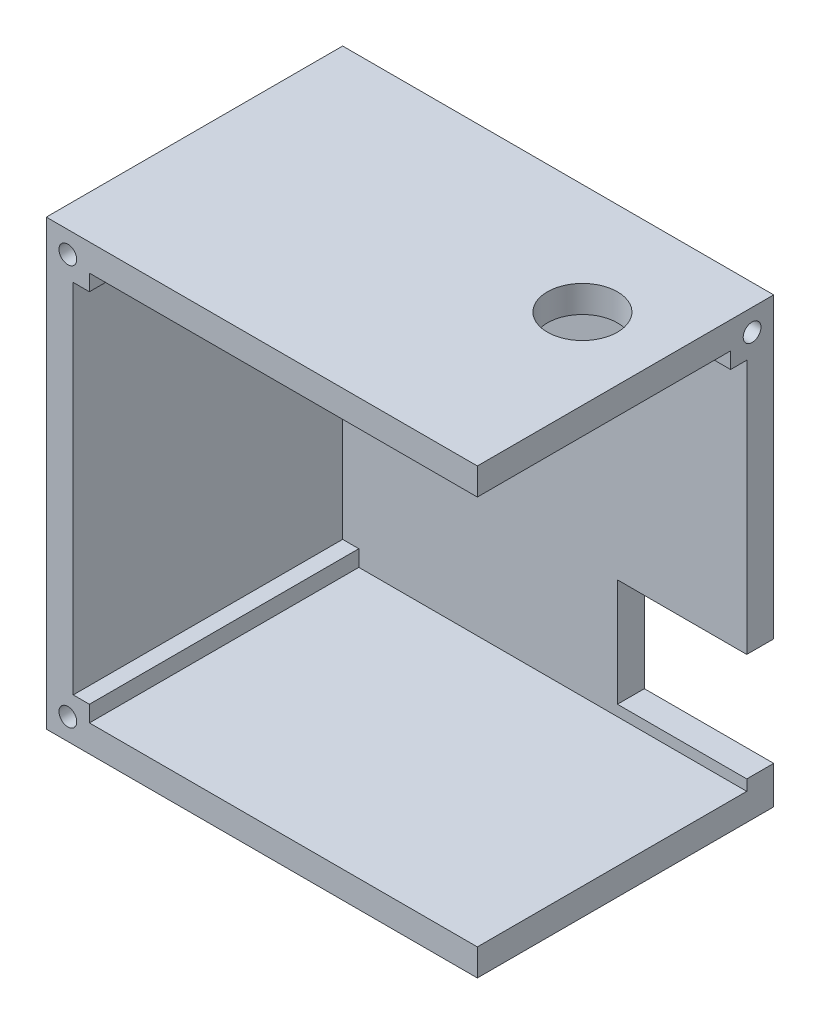
SolidWorks part; units mm, degrees
ref_plane "Front Plane" through (0, 0, 0) normal (0, 0, 1) x (1, 0, 0)
ref_plane "Top Plane" through (0, 0, 0) normal (0, 1, 0) x (1, 0, 0)
ref_plane "Right Plane" through (0, 0, 0) normal (1, 0, 0) x (0, 0, -1)
sketch "Sketch1" plane through (0, 0, 0) normal (0, 0, 1) x (1, 0, 0)
  line L1 (0, 0) -> (80, 0)
  line L2 (0, 0) -> (0, 82.3)
  line L3 (0, 82.3) -> (80, 82.3)
  line L4 (80, 0) -> (80, 82.3)
  dimension "D1" = 82.3
  dimension "D2" = 80
extrude "Boss-Extrude1" add sketch "Sketch1" along normal blind 55
sketch "Sketch2" plane through (0, 0, 55) normal (0, 0, 1) x (1, 0, 0)
  line L0 (80, 0) -> (80, 82.3) construction
  line L1 (5, 5) -> (80, 5) construction
  line L2 (5, 5) -> (5, 77.3) construction
  line L3 (5, 77.3) -> (80, 77.3) construction
  line L4 (80, 5) -> (80, 77.3)
  line L5 (80, 82.3) -> (0, 82.3) construction
  line L6 (0, 82.3) -> (0, 0) construction
  line L7 (5, 8) -> (5, 74.3)
  line L8 (5, 5) -> (8, 5) construction
  line L9 (5, 5) -> (5, 8) construction
  line L10 (5, 8) -> (8, 8)
  line L11 (8, 5) -> (8, 8)
  line L12 (5, 74.3) -> (8, 74.3)
  line L13 (5, 74.3) -> (5, 77.3) construction
  line L14 (5, 77.3) -> (8, 77.3) construction
  line L15 (8, 74.3) -> (8, 77.3)
  line L16 (8, 77.3) -> (80, 77.3)
  line L17 (8, 5) -> (80, 5)
  dimension "D1" = 5
  dimension "D2" = 5
  dimension "D3" = 5
  dimension "D4" = 3
extrude "Cut-Extrude1" cut sketch "Sketch2" against normal blind 50
sketch "Sketch3" plane through (0, 0, 55) normal (0, 0, 1) x (1, 0, 0)
  line L0 (4, 82.3) -> (4, 0) construction
  line L1 (80, 82.3) -> (0, 82.3) construction
  line L2 (0, 0) -> (80, 0) construction
  line L5 (0, 82.3) -> (0, 0) construction
  line L6 (4, 4) -> (4, 0) construction
  line L7 (4, 82.3) -> (4, 78.3) construction
  circle A0 centre (4, 78.3) radius 1.65
  circle A1 centre (4, 4) radius 1.65
  dimension "D3" = 3.3
  dimension "D1" = 4
  dimension "D2" = 4
extrude "Cut-Extrude2" cut sketch "Sketch3" against normal blind 25
sketch "Sketch4" plane through (0, 0, 5) normal (0, 0, 1) x (1, 0, 0)
  line L0 (5, 41.15) -> (80, 41.15) construction
  line L1 (5, 74.3) -> (5, 8) construction
  line L2 (80, 5) -> (80, 77.3) construction
  line L3 (8, 5) -> (80, 5) construction
  line L4 (10.5, 54.65) -> (25.5, 54.65)
  line L5 (10.5, 54.65) -> (10.5, 27.65)
  line L6 (10.5, 27.65) -> (25.5, 27.65)
  line L7 (25.5, 54.65) -> (25.5, 27.65)
  line L8 (56, 27) -> (80, 27)
  line L9 (56, 27) -> (56, 7)
  line L10 (56, 7) -> (80, 7)
  line L11 (80, 27) -> (80, 7)
  point P10 (25.5, 41.15)
  dimension "D1" = 27
  dimension "D2" = 15
  dimension "D3" = 5.5
  dimension "D4" = 24
  dimension "D5" = 20
  dimension "D6" = 2
extrude "Cut-Extrude3" cut sketch "Sketch4" against normal blind 20
sketch "Sketch6" plane through (0, 77.3, 0) normal (0, -1, 0) x (1, 0, 0)
  line L0 (8, 30) -> (80, 30) construction
  line L1 (8, 5) -> (8, 55) construction
  line L2 (80, 5) -> (80, 55) construction
  line L3 (80, 55) -> (80, 0) construction
  line L4 (0, 55) -> (80, 55) construction
  circle A0 centre (65, 20.5) radius 6.5
  dimension "D1" = 13
  dimension "D2" = 15
  dimension "D3" = 34.5
extrude "Cut-Extrude4" cut sketch "Sketch6" against normal blind 20
sketch "Sketch7" plane through (80, 0, 0) normal (1, 0, 0) x (0, 0, -1)
  line L0 (-5, 77.3) -> (-55, 77.3) construction
  line L1 (-8, 77.3) -> (-5, 77.3)
  line L2 (-8, 77.3) -> (-8, 74.3)
  line L3 (-8, 74.3) -> (-5, 74.3)
  line L4 (-5, 77.3) -> (-5, 74.3)
  line L5 (-5, 74.3) -> (-5, 8) construction
  line L6 (-5, 74.3) -> (-55, 74.3) construction
  dimension "D1" = 3
extrude "Boss-Extrude2" add sketch "Sketch7" against normal blind 30
sketch "Sketch8" plane through (80, 0, 0) normal (1, 0, 0) x (0, 0, -1)
  line L0 (-55, 82.3) -> (0, 82.3) construction
  line L1 (0, 27) -> (0, 82.3) construction
  circle A0 centre (-4.0046, 78.3) radius 1.65
  dimension "D1" = 3.3
  dimension "D2" = 4
  dimension "D3" = 4.0046
extrude "Cut-Extrude5" cut sketch "Sketch8" against normal blind 25
